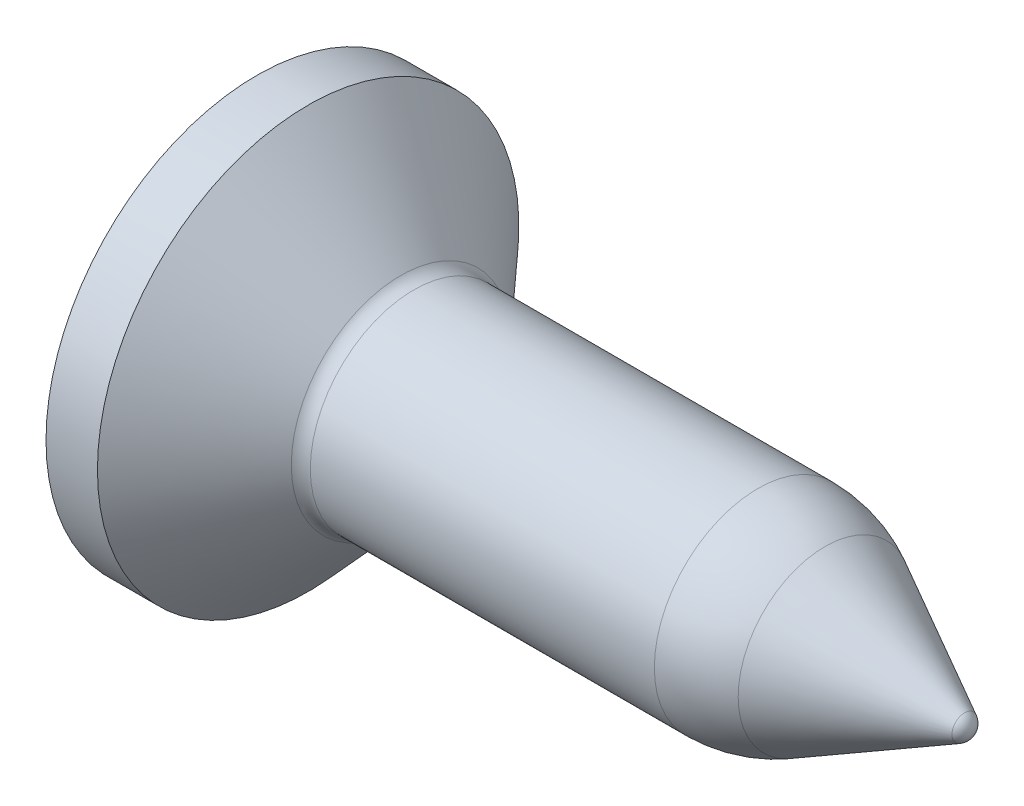
SolidWorks part; units mm, degrees
ref_plane "Front" through (0, 0, 0) normal (0, 0, 1) x (1, 0, 0)
ref_plane "Top" through (0, 0, 0) normal (0, 1, 0) x (1, 0, 0)
ref_plane "Right" through (0, 0, 0) normal (1, 0, 0) x (0, 0, -1)
sketch "Sketch1" plane through (0, 0, 0) normal (0, 0, 1) x (1, 0, 0)
  line L0 (0, 0) -> (0, 2.95)
  line L1 (0, 2.95) -> (0.72, 2.95)
  line L2 (0.72, 2.95) -> (2.0154, 1.5314)
  line L3 (2.2, 1.45) -> (7.0165, 1.45)
  line L6 (10.0154, 0) -> (0, 0)
  line L7 (-3.9747, 0) -> (0, 0) construction
  line L8 (9.9093, 0.1766) -> (7.9558, 1.2157)
  arc A0 (2.0154, 1.5314) -> (2.2, 1.45) centre (2.2, 1.7) ccw
  arc A2 (9.9093, 0.1766) -> (10.0154, 0) centre (9.8154, 0) cw
  arc A3 (7.0165, 1.45) -> (7.9558, 1.2157) centre (7.0165, -0.55) cw
  point P13 (7.5154, 1.45)
  dimension "D3" = 0.25
  dimension "D1" = 0.2
  dimension "D8" = 2
  dimension "D2" = 2.9
  dimension "D4" = 2.2
  dimension "D5" = 0.72
  dimension "D6" = 2.5
  dimension "D7" = 8
  dimension "D9" = 5.9
revolve "Revolve1" add sketch "Sketch1" angle 360 about L7
sketch "Sketch2" plane through (0, 0, 0) normal (-1, 0, 0) x (0, 0, 1)
  line L0 (1.5, 0) -> (0, 0) construction
  line L1 (0, 0) -> (0, 1.5) construction
  line L2 (-0.25, 1.5) -> (0.25, 1.5)
  line L3 (0.25, 1.5) -> (0.4374, 0.4374)
  line L4 (0.4374, 0.4374) -> (1.5, 0.25)
  line L5 (1.5, 0.25) -> (1.5, -0.25)
  line L6 (-0.25, 1.5) -> (-0.4374, 0.4374)
  line L7 (-0.4374, 0.4374) -> (-1.5, 0.25)
  line L8 (-1.5, 0.25) -> (-1.5, -0.25)
  line L9 (-0.4374, -0.4374) -> (-1.5, -0.25)
  line L10 (-0.25, -1.5) -> (-0.4374, -0.4374)
  line L11 (-0.25, -1.5) -> (0.25, -1.5)
  line L12 (0.25, -1.5) -> (0.4374, -0.4374)
  line L13 (0.4374, -0.4374) -> (1.5, -0.25)
  point P12 (-1.5, 0)
  dimension "D1" = 100
  dimension "D2" = 3
  dimension "D3" = 0.5
extrude "Cut-Extrude1" cut sketch "Sketch2" against normal blind 0.5
